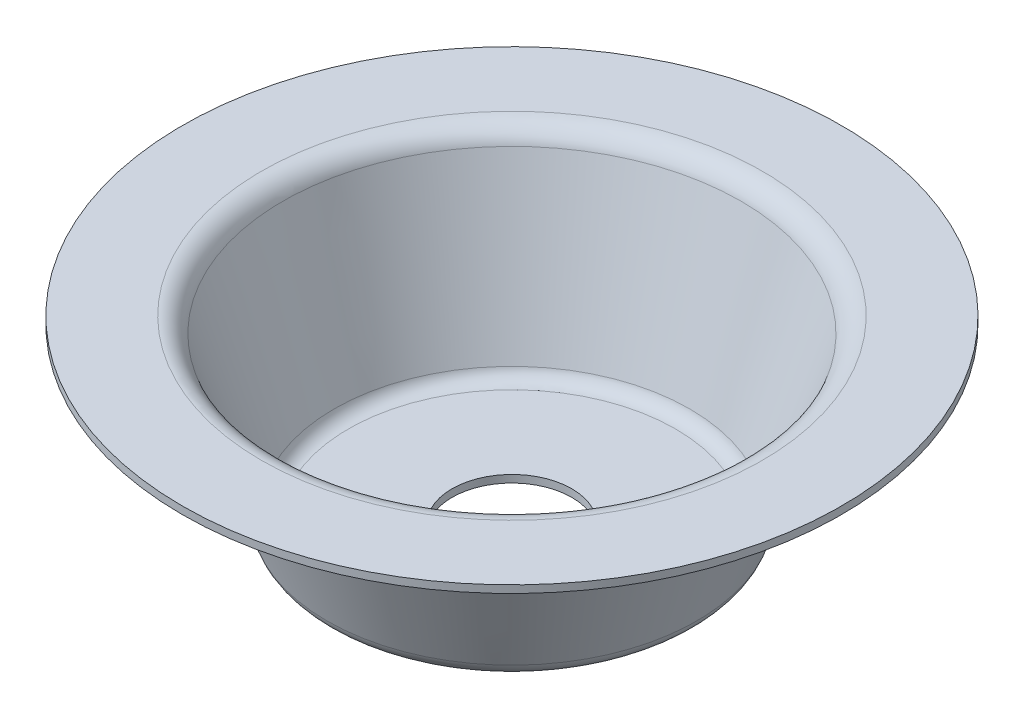
SolidWorks part; units mm, degrees
material "3003 Alloy"
ref_plane "Front Plane" through (0, 0, 0) normal (0, 0, 1) x (1, 0, 0)
ref_plane "Top Plane" through (0, 0, 0) normal (0, 1, 0) x (1, 0, 0)
ref_plane "Right Plane" through (0, 0, 0) normal (1, 0, 0) x (0, 0, -1)
sketch "Sketch1" plane through (0, 0, 0) normal (0, 0, 1) x (1, 0, 0)
  line L0 (0, 0) -> (-34.6674, 0)
  line L1 (-39.1855, 3.2565) -> (-50.0763, 35.929)
  line L2 (-53.0884, 38.1) -> (-69.85, 38.1)
  line L3 (0, 40.5013) -> (0, 0) construction
  arc A0 (-34.6674, 0) -> (-39.1855, 3.2565) centre (-34.6674, 4.7625) cw
  arc A1 (-50.0763, 35.929) -> (-53.0884, 38.1) centre (-53.0884, 34.925) ccw
  point P8 (-38.1, 0)
  point P11 (-50.8, 38.1)
  dimension "D5" = 4.7625
  dimension "D6" = 3.175
  dimension "D1" = 76.2
  dimension "D2" = 101.6
  dimension "D3" = 38.1
  dimension "D4" = 139.7
revolve "Revolve-Thin1" add sketch "Sketch1" angle 360 about L3
sketch "Sketch2" plane through (0, 0, 0) normal (0, -1, 0) x (1, 0, 0)
  circle A0 centre (0, 0) radius 12.7
  dimension "D1" = 25.4
extrude "Cut-Extrude1" cut sketch "Sketch2" against normal through all
